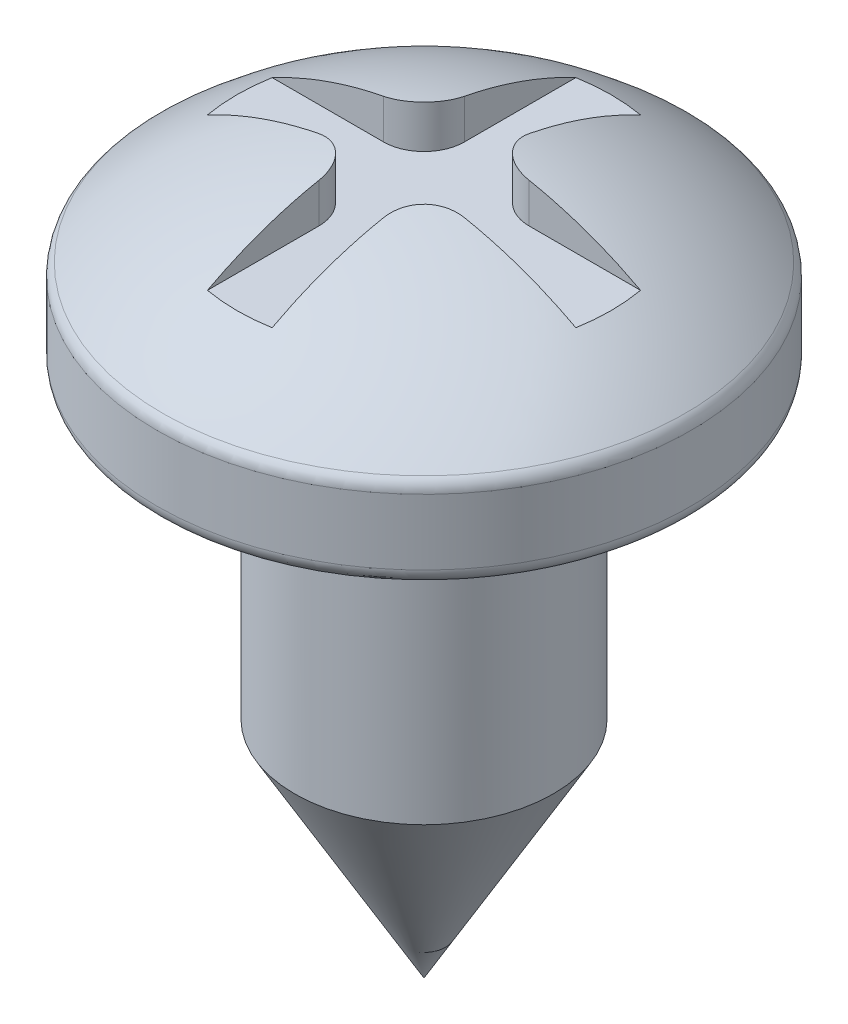
SolidWorks part; units mm, degrees
material "acero"
ref_plane "Alzado" through (0, 0, 0) normal (0, 0, 1) x (1, 0, 0)
ref_plane "Planta" through (0, 0, 0) normal (0, 1, 0) x (1, 0, 0)
ref_plane "Vista lateral" through (0, 0, 0) normal (1, 0, 0) x (0, 0, -1)
sketch "Croquis1" plane through (0, 0, 0) normal (0, 0, 1) x (1, 0, 0)
  line L0 (0, 0) -> (0, 8.9) construction
  line L1 (0, 0) -> (0, 8.9)
  line L2 (3.3, 6.7) -> (3.3, 7.5104)
  line L3 (3.1, 6.5) -> (1.6, 6.5)
  line L4 (1.6, 6.5) -> (1.6, 2.7713)
  line L5 (1.6, 2.7713) -> (0, 0)
  arc A0 (3.1, 6.5) -> (3.3, 6.7) centre (3.1, 6.7) ccw
  arc A1 (3.2318, 7.6609) -> (0, 8.9) centre (-0.0635, 3.9004) ccw
  arc A2 (3.3, 7.5104) -> (3.2318, 7.6609) centre (3.1, 7.5104) ccw
  point P11 (3.3, 6.5)
  point P14 (3.3, 7.6)
  dimension "D7" = 0.2
  dimension "D8" = 5
  dimension "D1" = 8.9
  dimension "D2" = 30
  dimension "D3" = 1.1
  dimension "D4" = 1.6
  dimension "D5" = 3.3
  dimension "D9" = 6.5
revolve "Revolución1" add sketch "Croquis1" angle 360 about L0
sketch "Croquis2" plane through (0, 6.5, 0) normal (0, -1, 0) x (1, 0, 0)
  line L0 (0, 0) -> (0, 3.3) construction
  line L1 (-0.4, 3.2) -> (-0.4, 0.9)
  line L2 (-0.9, 0.4) -> (-3.2, 0.4)
  line L3 (-3.2, 0.4) -> (-3.2, -0.4)
  line L4 (-3.2, -0.4) -> (-0.9, -0.4)
  line L5 (-0.4, -0.9) -> (-0.4, -3.2)
  line L6 (-0.4, -3.2) -> (0.4, -3.2)
  line L7 (0.4, -3.2) -> (0.4, -0.9)
  line L8 (0.9, -0.4) -> (3.2, -0.4)
  line L9 (3.2, -0.4) -> (3.2, 0.4)
  line L10 (3.2, 0.4) -> (0.9, 0.4)
  line L11 (0.4, 0.9) -> (0.4, 3.2)
  line L12 (0.4, 3.2) -> (-0.4, 3.2)
  circle A0 centre (0, 0) radius 3.3 construction
  arc A1 (-0.4, -0.9) -> (-0.9, -0.4) centre (-0.9, -0.9) ccw
  arc A2 (0.4, -0.9) -> (0.9, -0.4) centre (0.9, -0.9) cw
  arc A3 (0.9, 0.4) -> (0.4, 0.9) centre (0.9, 0.9) cw
  arc A4 (-0.9, 0.4) -> (-0.4, 0.9) centre (-0.9, 0.9) ccw
  point P26 (-0.4, 0.4)
  dimension "D12" = 0.5
  dimension "D1" = 0.4
  dimension "D2" = 0.8
  dimension "D3" = 3.2
  dimension "D4" = 3.2
  dimension "D5" = 3.2
  dimension "D6" = 3.2
  dimension "D7" = 0.4
  dimension "D8" = 0.4
  dimension "D9" = 0.4
  dimension "D10" = 0.4
  dimension "D11" = 0.4
extrude "Cortar-Extruir1" cut sketch "Croquis2" against normal blind 3 from offset 1.8
